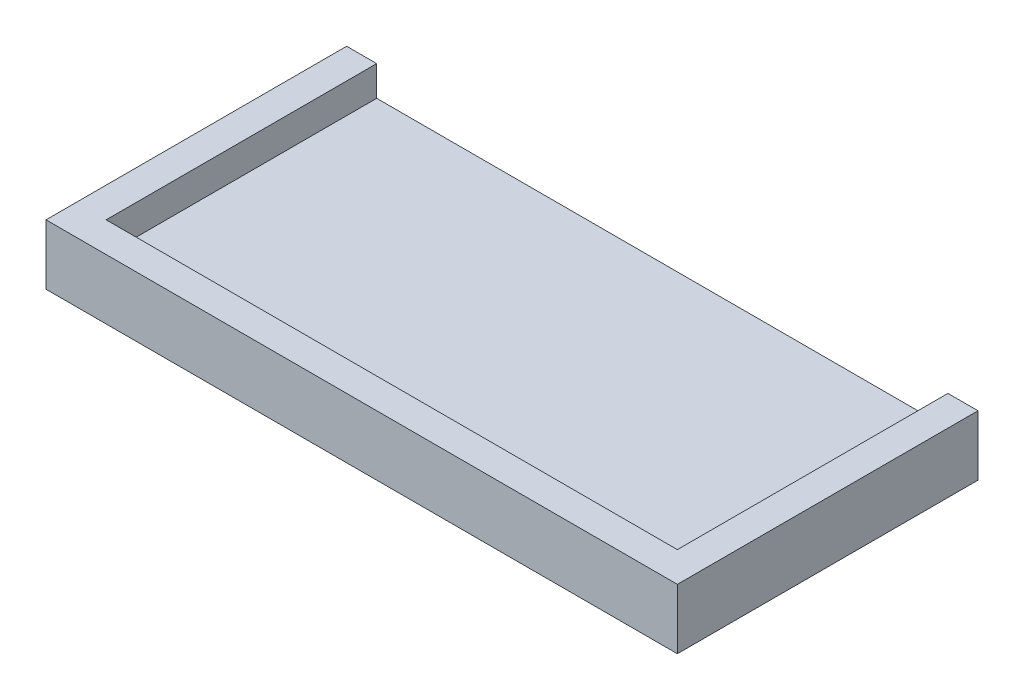
SolidWorks part; units mm, degrees
ref_plane "Front Plane" through (0, 0, 0) normal (0, 0, 1) x (1, 0, 0)
ref_plane "Top Plane" through (0, 0, 0) normal (0, 1, 0) x (1, 0, 0)
ref_plane "Right Plane" through (0, 0, 0) normal (1, 0, 0) x (0, 0, -1)
sketch "Sketch1" plane through (0, 0, 0) normal (0, 1, 0) x (1, 0, 0)
  line L1 (-52.5, -25) -> (52.5, -25)
  line L2 (-52.5, -25) -> (-52.5, 25)
  line L3 (-52.5, 25) -> (52.5, 25)
  line L4 (52.5, -25) -> (52.5, 25)
  line L5 (-52.5, -25) -> (52.5, 25) construction
  line L6 (-52.5, 25) -> (52.5, -25) construction
  point P0 (0, 0)
  dimension "D1" = 105
  dimension "D2" = 50
extrude "Boss-Extrude1" add sketch "Sketch1" along normal blind 5
sketch "Sketch2" plane through (0, 5, 0) normal (0, 1, 0) x (1, 0, 0)
  line L0 (-52.5, 25) -> (-52.5, -25)
  line L1 (-52.5, -25) -> (52.5, -25)
  line L2 (52.5, -25) -> (52.5, 25)
  line L3 (52.5, 25) -> (47.5, 25)
  line L4 (52.5, 25) -> (-52.5, 25) construction
  line L5 (47.5, 25) -> (47.5, -20)
  line L6 (47.5, -20) -> (-47.5, -20)
  line L7 (-47.5, -20) -> (-47.5, 25)
  line L8 (-47.5, 25) -> (-52.5, 25)
  dimension "D1" = 5
  dimension "D2" = 5
  dimension "D3" = 5
extrude "Boss-Extrude2" add sketch "Sketch2" along normal blind 5
sketch "Sketch3" plane through (0, 5, 0) normal (0, 1, 0) x (1, 0, 0)
  text T0 "<b><i>PillPal</i></b>"
